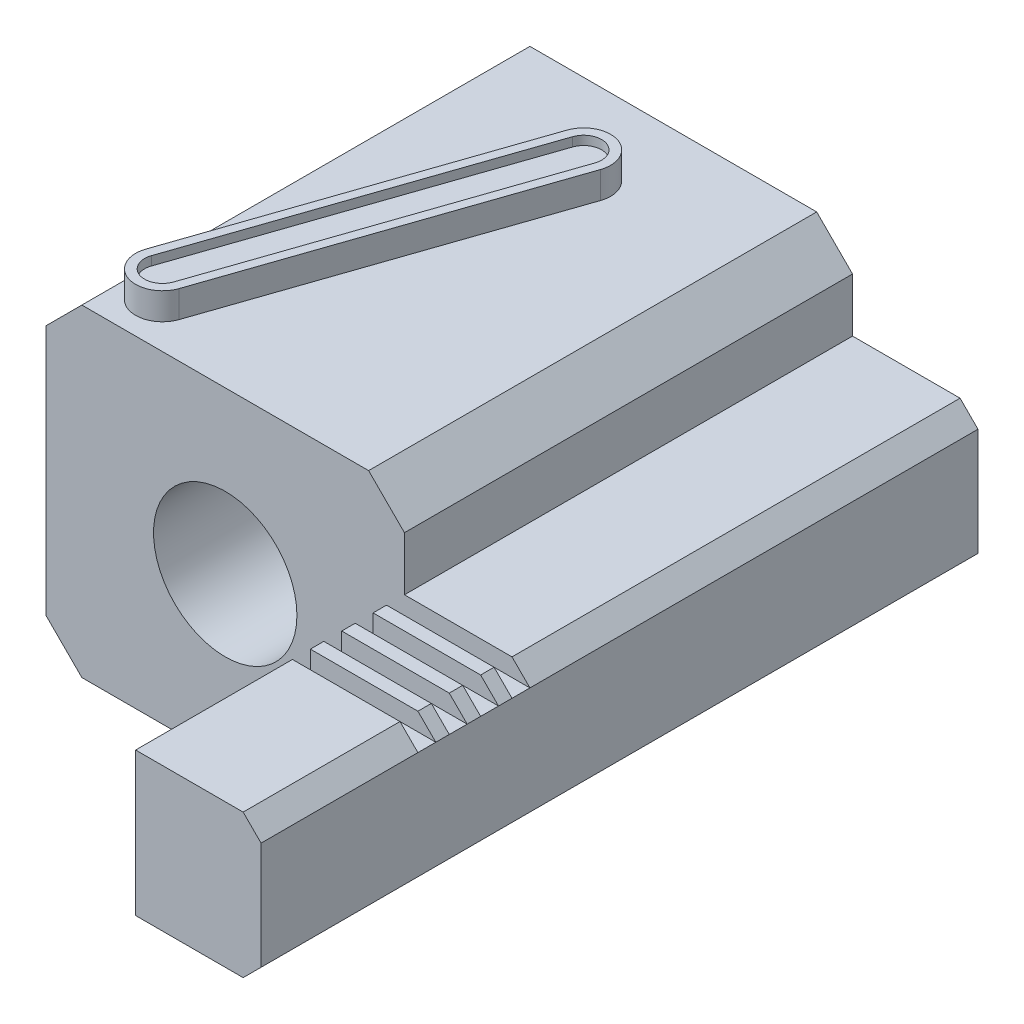
SolidWorks part; units mm, degrees
ref_plane "Front Plane" through (0, 0, 0) normal (0, 0, 1) x (1, 0, 0)
ref_plane "Top Plane" through (0, 0, 0) normal (0, 1, 0) x (1, 0, 0)
ref_plane "Right Plane" through (0, 0, 0) normal (1, 0, 0) x (0, 0, -1)
sketch "Sketch1" plane through (0, 0, 0) normal (0, 0, 1) x (1, 0, 0)
  line L0 (-10, 9) -> (-10, -9)
  line L1 (-10, 9) -> (10, 9)
  line L2 (-10, -9) -> (10, -9)
  line L3 (10, 9) -> (10, -9)
  line L4 (-10, 9) -> (10, -9) construction
  dimension "D1" = 20
  dimension "D2" = 18
extrude "Boss-Extrude1" add sketch "Sketch1" along normal blind 25
sketch "Sketch2" plane through (0, 0, 25) normal (0, 0, 1) x (1, 0, 0)
  circle A1 centre (0, 0) radius 4
  dimension "D3" = 8
extrude "Cut-Extrude1" cut sketch "Sketch2" against normal through all
chamfer "Chamfer1" distance 2 angle 45 4 edges at (-10, 9, 12.5) (-10, -9, 12.5) (10, -9, 12.5) (10, 9, 12.5)
sketch "Sketch3" plane through (0, 9, 0) normal (0, 1, 0) x (1, 0, 0)
  line L0 (-6, -22.5) -> (0, -5) construction
  line L1 (-7.4189, -22.0135) -> (-1.4189, -4.5135)
  line L2 (-4.5811, -22.9865) -> (1.4189, -5.4865)
  line L3 (8, -25) -> (-8, -25) construction
  line L5 (-10, -25) -> (-10, 0) construction
  line L6 (8, 0) -> (-8, 0) construction
  arc A0 (-7.4189, -22.0135) -> (-4.5811, -22.9865) centre (-6, -22.5) ccw
  arc A1 (1.4189, -5.4865) -> (-1.4189, -4.5135) centre (0, -5) ccw
  point P2 (-3, -13.75)
  dimension "D1" = 3
  dimension "D2" = 2.5
  dimension "D3" = 4
  dimension "D4" = 5
  dimension "D5" = 10
extrude "Boss-Extrude2" add sketch "Sketch3" along normal blind 1.5
sketch "Sketch4" plane through (0, 10.5, 0) normal (0, 1, 0) x (1, 0, 0)
  line L0 (-6, -22.5) -> (0, -5) construction
  line L1 (-6.9459, -22.1757) -> (-0.9459, -4.6757)
  line L2 (-5.0541, -22.8243) -> (0.9459, -5.3243)
  arc A0 (-6.9459, -22.1757) -> (-5.0541, -22.8243) centre (-6, -22.5) ccw
  arc A1 (0.9459, -5.3243) -> (-0.9459, -4.6757) centre (0, -5) ccw
  point P4 (-3, -13.75)
  dimension "D1" = 2
extrude "Cut-Extrude2" cut sketch "Sketch4" against normal blind 0.5
sketch "Sketch5" plane through (0, 0, 0) normal (0, 0, -1) x (-1, 0, 0)
  line L0 (-10, 4) -> (-16, 4)
  line L1 (-10, -7) -> (-10, 7) construction
  line L2 (-16, 4) -> (-17, 3)
  line L3 (-17, 3) -> (-17, -3)
  line L4 (-17, -3) -> (-16, -4)
  line L5 (-16, -4) -> (-10, -4)
  line L6 (-10, -4) -> (-10, 4)
  line L7 (0, 0) -> (-17, 0) construction
  line L8 (-10, 0) -> (0, 0) construction
  dimension "D1" = 1
  dimension "D2" = 7
  dimension "D3" = 8
extrude "Boss-Extrude3" add sketch "Sketch5" against normal blind 40
sketch "Sketch6" plane through (10, 0, 0) normal (-1, 0, 0) x (0, 0, 1)
  line L0 (40, 4) -> (25, 4) construction
  line L1 (25, 4) -> (26, 4)
  line L2 (25, 4) -> (25, 3)
  line L3 (25, 3) -> (26, 3)
  line L4 (26, 4) -> (26, 3)
  line L5 (26, 3) -> (26.75, 3) construction
  line L6 (26.75, 4) -> (27.75, 4)
  line L7 (26.75, 4) -> (26.75, 3)
  line L8 (26.75, 3) -> (27.75, 3)
  line L9 (27.75, 4) -> (27.75, 3)
  line L10 (28.5, 4) -> (29.5, 4)
  line L11 (28.5, 4) -> (28.5, 3)
  line L12 (28.5, 3) -> (29.5, 3)
  line L13 (29.5, 4) -> (29.5, 3)
  line L14 (30.25, 4) -> (31.25, 4)
  line L15 (30.25, 4) -> (30.25, 3)
  line L16 (30.25, 3) -> (31.25, 3)
  line L17 (31.25, 4) -> (31.25, 3)
  line L18 (27.75, 3) -> (28.5, 3) construction
  line L19 (25, -4) -> (25, 4) construction
  line L20 (29.5, 3) -> (30.25, 3) construction
  line L21 (25, 0) -> (40, 0) construction
  line L22 (40, -4) -> (40, 4) construction
  dimension "D1" = 1
  dimension "D2" = 0.75
  dimension "D3" = 1
extrude "Cut-Extrude3" cut sketch "Sketch6" against normal through all
